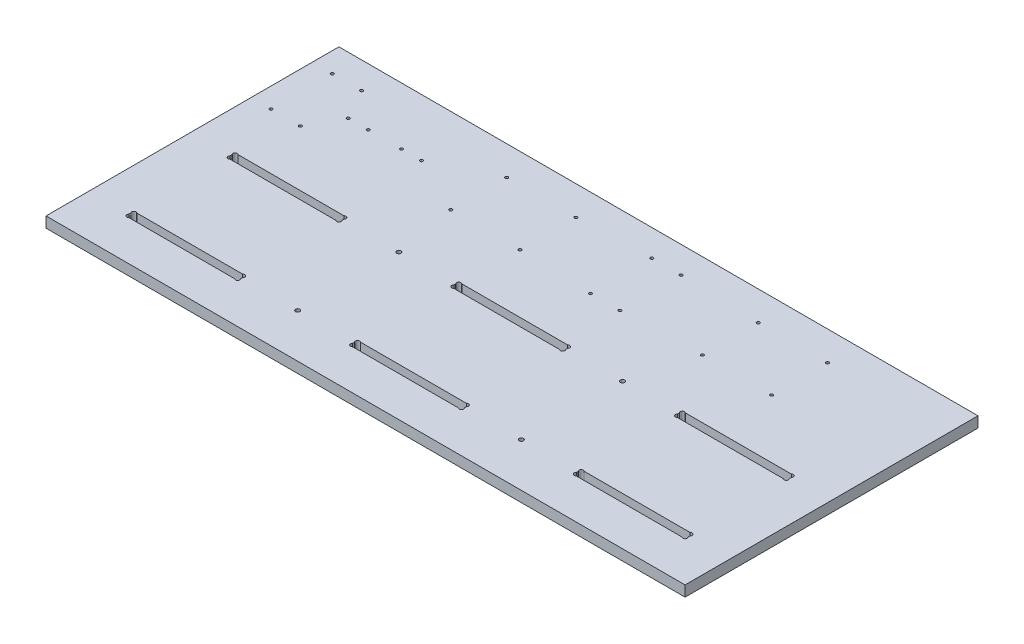
SolidWorks part; units mm, degrees
ref_plane "Plan de face" through (0, 0, 0) normal (0, 0, 1) x (1, 0, 0)
ref_plane "Plan de dessus" through (0, 0, 0) normal (0, 1, 0) x (1, 0, 0)
ref_plane "Plan de droite" through (0, 0, 0) normal (1, 0, 0) x (0, 0, -1)
sketch "Esquisse1" plane through (0, 0, 0) normal (0, 1, 0) x (1, 0, 0)
  line L0 (-31.0898, 0) -> (555.237, 0) construction
  line L1 (10, 0) -> (490, 0)
  line L2 (25, 200) -> (457.7373, 200) construction
  line L3 (10, 220) -> (490, 220)
  line L4 (490, 0) -> (490, 220)
  line L5 (0, -11.0942) -> (0, 294.931) construction
  line L6 (500, -11.0942) -> (500, 294.931) construction
  line L7 (-31.0898, 220) -> (555.237, 220) construction
  line L8 (-31.0898, 30) -> (531.4772, 30) construction
  line L9 (490, -11.0942) -> (490, 262.6177) construction
  line L10 (40, -46.1012) -> (40, 236.6995) construction
  line L11 (250, 278.7744) -> (250, -46.1012) construction
  line L12 (-31.0898, 110) -> (265.8436, 110) construction
  line L13 (531.4772, 36) -> (27.503, 36) construction
  line L14 (531.4772, 106) -> (27.503, 106) construction
  line L15 (531.4772, 112) -> (27.503, 112) construction
  line L16 (124, -46.1012) -> (124, 56.1605) construction
  line L17 (208, -46.1012) -> (208, 56.1605) construction
  line L18 (82, 56.1605) -> (82, -21.9054) construction
  line L19 (27.503, 71) -> (195.5043, 71) construction
  line L20 (55.6013, 33) -> (87.5, 33) construction
  line L21 (124, 36) -> (90.2459, 2.2459) construction
  line L22 (166, 52.2816) -> (166, -21.9054) construction
  line L23 (40, 33.7373) -> (40, 32.2627)
  line L24 (42.2627, 30) -> (121.7373, 30)
  line L25 (124, 32.2627) -> (124, 33.7373)
  line L26 (121.7373, 36) -> (42.2627, 36)
  line L27 (378.2627, 36) -> (457.7373, 36)
  line L28 (376, 32.2627) -> (376, 33.7373)
  line L29 (457.7373, 30) -> (378.2627, 30)
  line L30 (460, 33.7373) -> (460, 32.2627)
  line L31 (208, 33.7373) -> (208, 32.2627)
  line L32 (210.2627, 36) -> (289.7373, 36)
  line L33 (292, 33.7373) -> (292, 32.2627)
  line L34 (289.7373, 30) -> (210.2627, 30)
  line L35 (289.7373, 112) -> (210.2627, 112)
  line L36 (292, 108.2627) -> (292, 109.7373)
  line L37 (210.2627, 106) -> (289.7373, 106)
  line L38 (208, 108.2627) -> (208, 109.7373)
  line L39 (460, 108.2627) -> (460, 109.7373)
  line L40 (457.7373, 112) -> (378.2627, 112)
  line L41 (376, 109.7373) -> (376, 108.2627)
  line L42 (378.2627, 106) -> (457.7373, 106)
  line L43 (121.7373, 106) -> (42.2627, 106)
  line L44 (124, 109.7373) -> (124, 108.2627)
  line L45 (42.2627, 112) -> (121.7373, 112)
  line L46 (40, 108.2627) -> (40, 109.7373)
  line L47 (10, 258.341) -> (10, -46.1012) construction
  line L48 (10, 220) -> (10, 0)
  line L50 (158, 236.6995) -> (158, 135.7937) construction
  line L51 (210, 236.6995) -> (210, 135.7937) construction
  line L53 (189.5651, 177) -> (50.5313, 177) construction
  line L55 (87.5, 254.587) -> (87.5, 160.1956) construction
  line L56 (60, 241.0582) -> (60, 170.7991) construction
  line L57 (75, 230.6402) -> (75, 170.7991) construction
  arc A0 (124, 33.7373) -> (121.7373, 36) centre (122.8686, 34.8686) ccw
  arc A1 (124, 32.2627) -> (121.7373, 30) centre (122.8686, 31.1314) cw
  arc A2 (40, 33.7373) -> (42.2627, 36) centre (41.1314, 34.8686) cw
  arc A3 (40, 32.2627) -> (42.2627, 30) centre (41.1314, 31.1314) ccw
  arc A4 (208, 33.7373) -> (210.2627, 36) centre (209.1314, 34.8686) cw
  arc A5 (208, 32.2627) -> (210.2627, 30) centre (209.1314, 31.1314) ccw
  arc A6 (292, 32.2627) -> (289.7373, 30) centre (290.8686, 31.1314) cw
  arc A7 (292, 33.7373) -> (289.7373, 36) centre (290.8686, 34.8686) ccw
  arc A8 (460, 32.2627) -> (457.7373, 30) centre (458.8686, 31.1314) cw
  arc A9 (460, 33.7373) -> (457.7373, 36) centre (458.8686, 34.8686) ccw
  arc A10 (376, 32.2627) -> (378.2627, 30) centre (377.1314, 31.1314) ccw
  arc A11 (376, 33.7373) -> (378.2627, 36) centre (377.1314, 34.8686) cw
  arc A12 (376, 108.2627) -> (378.2627, 106) centre (377.1314, 107.1314) ccw
  arc A13 (376, 109.7373) -> (378.2627, 112) centre (377.1314, 110.8686) cw
  arc A14 (460, 108.2627) -> (457.7373, 106) centre (458.8686, 107.1314) cw
  arc A15 (460, 109.7373) -> (457.7373, 112) centre (458.8686, 110.8686) ccw
  arc A16 (292, 108.2627) -> (289.7373, 106) centre (290.8686, 107.1314) cw
  arc A17 (292, 109.7373) -> (289.7373, 112) centre (290.8686, 110.8686) ccw
  arc A18 (208, 109.7373) -> (210.2627, 112) centre (209.1314, 110.8686) cw
  arc A19 (208, 108.2627) -> (210.2627, 106) centre (209.1314, 107.1314) ccw
  arc A20 (40, 109.7373) -> (42.2627, 112) centre (41.1314, 110.8686) cw
  arc A21 (40, 108.2627) -> (42.2627, 106) centre (41.1314, 107.1314) ccw
  arc A22 (124, 109.7373) -> (121.7373, 112) centre (122.8686, 110.8686) ccw
  arc A23 (124, 108.2627) -> (121.7373, 106) centre (122.8686, 107.1314) cw
  circle A24 centre (166, 33) radius 1.6
  circle A25 centre (334, 33) radius 1.6
  circle A26 centre (334, 109) radius 1.6
  circle A27 centre (166, 109) radius 1.6
  circle A28 centre (158, 198) radius 1.1
  circle A29 centre (210, 198) radius 1.1
  circle A30 centre (210, 156) radius 1.1
  circle A31 centre (158, 156) radius 1.1
  circle A32 centre (60, 177) radius 1.1
  circle A33 centre (75, 177) radius 1.1
  circle A34 centre (100, 177) radius 1.1
  circle A35 centre (115, 177) radius 1.1
  circle A36 centre (25, 200) radius 1.1
  circle A37 centre (47, 200) radius 1.1
  circle A38 centre (47, 154) radius 1.1
  circle A39 centre (25, 154) radius 1.1
  circle A40 centre (287, 200) radius 1.1
  circle A41 centre (287, 154) radius 1.1
  circle A42 centre (265, 200) radius 1.1
  circle A43 centre (265, 154) radius 1.1
  circle A44 centre (399, 156) radius 1.1
  circle A45 centre (347, 198) radius 1.1
  circle A46 centre (347, 156) radius 1.1
  circle A47 centre (399, 198) radius 1.1
  dimension "D17" = 42
  dimension "D18" = 52
  dimension "D22" = 20
  dimension "D28" = 22
  dimension "D24" = 2.2
  dimension "D1" = 500
  dimension "D2" = 220
  dimension "D3" = 110
  dimension "D4" = 30
  dimension "D5" = 250
  dimension "D6" = 30
  dimension "D7" = 10
  dimension "D8" = 6
  dimension "D9" = 70
  dimension "D10" = 6
  dimension "D11" = 84
  dimension "D12" = 42
  dimension "D13" = 45
  dimension "D14" = 42
  dimension "D15" = 3
  dimension "D16" = 35
  dimension "D19" = 42
  dimension "D20" = 22
  dimension "D21" = 148
  dimension "D23" = 15
  dimension "D25" = 46
  dimension "D26" = 27.5
  dimension "D27" = 15
  dimension "D29" = 42
  dimension "D30" = 22
  dimension "D31" = 22
  dimension "D32" = 42
extrude "Boss.-Extru.1" add sketch "Esquisse1" along normal blind 8
